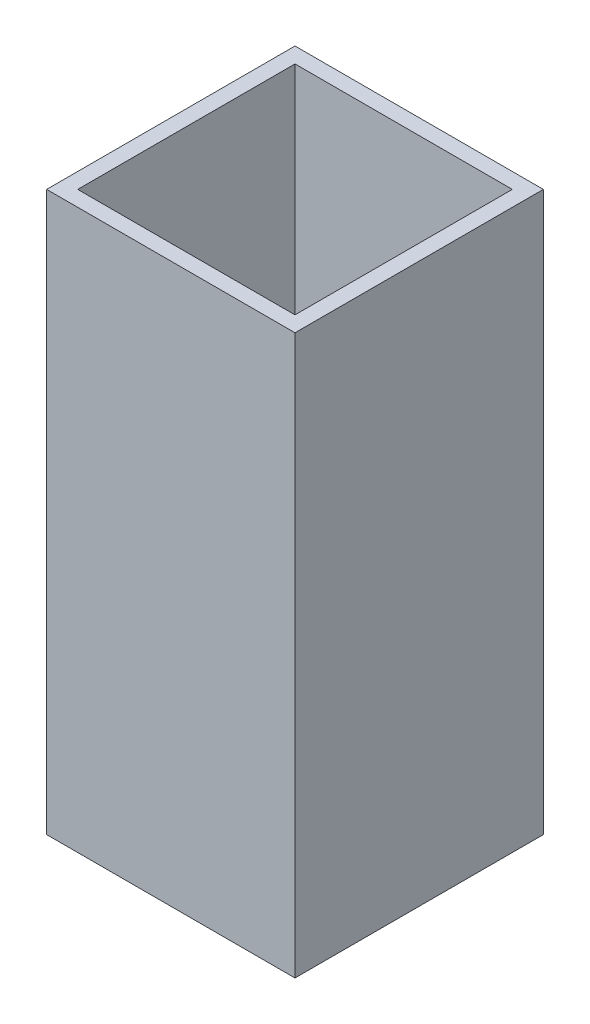
SolidWorks part; units mm, degrees
material "6061 Alloy"
ref_plane "Front Plane" through (0, 0, 0) normal (0, 0, 1) x (1, 0, 0)
ref_plane "Top Plane" through (0, 0, 0) normal (0, 1, 0) x (1, 0, 0)
ref_plane "Right Plane" through (0, 0, 0) normal (1, 0, 0) x (0, 0, -1)
sketch "Sketch1" plane through (0, 0, 0) normal (0, 1, 0) x (1, 0, 0)
  line L0 (22.225, -22.225) -> (22.225, 22.225)
  line L1 (25.4, -25.4) -> (-25.4, -25.4)
  line L2 (25.4, -25.4) -> (25.4, 25.4)
  line L3 (25.4, 25.4) -> (-25.4, 25.4)
  line L4 (-25.4, -25.4) -> (-25.4, 25.4)
  line L5 (25.4, -25.4) -> (-25.4, 25.4) construction
  line L6 (25.4, 25.4) -> (-25.4, -25.4) construction
  line L7 (22.225, 22.225) -> (-22.225, 22.225)
  line L8 (-22.225, -22.225) -> (-22.225, 22.225)
  line L9 (22.225, -22.225) -> (-22.225, -22.225)
  point P0 (0, 0)
  dimension "D1" = 50.8
  dimension "D2" = 50.8
  dimension "D3" = 3.175
extrude "Boss-Extrude1" add sketch "Sketch1" along normal blind 114.3
